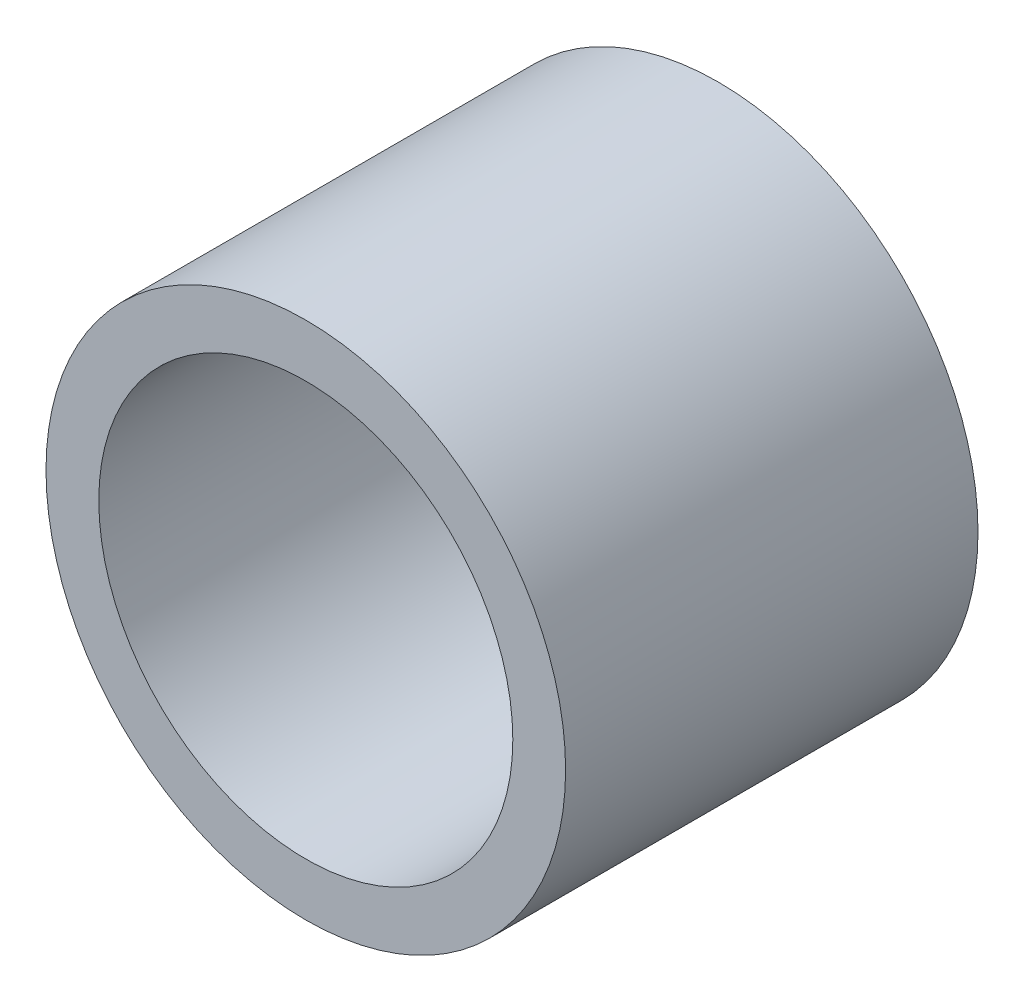
SolidWorks part; units mm, degrees
material "Phosphor bronze 10% D, UNS C52400"
ref_plane "Front Plane" through (0, 0, 0) normal (0, 0, 1) x (1, 0, 0)
ref_plane "Top Plane" through (0, 0, 0) normal (0, 1, 0) x (1, 0, 0)
ref_plane "Right Plane" through (0, 0, 0) normal (1, 0, 0) x (0, 0, -1)
sketch "Sketch1" plane through (0, 0, 0) normal (0, 0, 1) x (1, 0, 0)
  circle A0 centre (0, 0) radius 4.0005
  circle A1 centre (0, 0) radius 3.1877
  dimension "ID" = 6.3754
  dimension "OD" = 8.001
extrude "Boss-Extrude1" add sketch "Sketch1" along normal mid plane 6.35
sketch "Sketch2" plane through (0, 0, 0) normal (1, 0, 0) x (0, 0, -1)
  line L0 (-3.175, 4.0005) -> (3.175, 4.0005)
  line L1 (-3.175, 0) -> (3.175, 0) construction
  line L2 (-3.175, 4.0005) -> (-3.175, -4.0005) construction
  line L3 (3.175, -4.0005) -> (3.175, 4.0005) construction
  dimension "D1" = 8.001
  dimension "D2" = 6.35
equation "\"D1@Sketch2\"=\"OD@Sketch1\""
